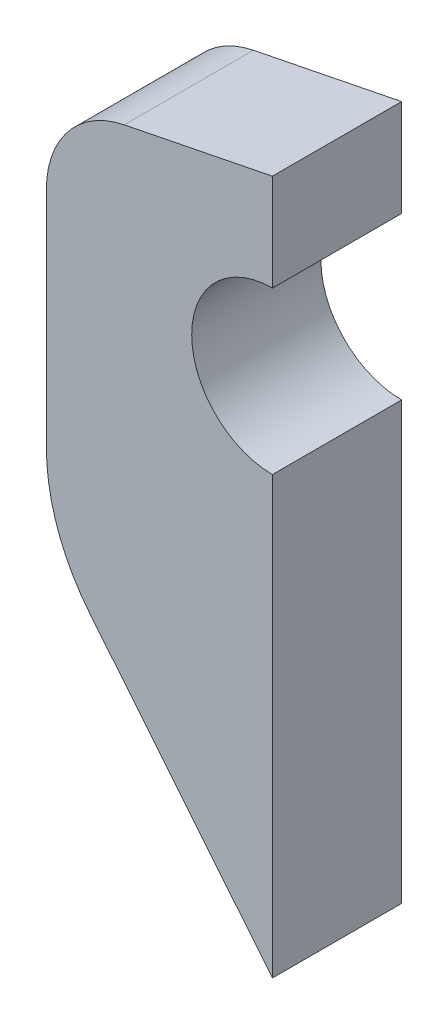
SolidWorks part; units mm, degrees
material "ﾊﾞﾙｻ"
ref_plane "正面" through (0, 0, 0) normal (0, 0, 1) x (1, 0, 0)
ref_plane "平面" through (0, 0, 0) normal (0, 1, 0) x (1, 0, 0)
ref_plane "右側面" through (0, 0, 0) normal (1, 0, 0) x (0, 0, -1)
sketch "ｽｹｯﾁ1" plane through (0, 0, 0) normal (0, 0, 1) x (1, 0, 0)
  line L0 (0, 5.5) -> (-15, 2.5)
  line L1 (-15, 2.5) -> (-15, -16)
  line L2 (-15, -16) -> (0, -16)
  line L3 (0, -16) -> (0, 5.5)
  line L4 (-15, 2.5) -> (0, 2.5) construction
  line L9 (0, -16) -> (-7, -7.4)
  line L10 (-7, -7.4) -> (-7, 4.1)
  circle A0 centre (0, 0) radius 2.5
  point P7 (-6.3571, -7.7069)
  point P8 (-10, -6)
  dimension "D1" = 5
  dimension "D2" = 10
  dimension "D3" = 3
  dimension "D4" = 15
  dimension "D5" = 6
  dimension "D6" = 16
  dimension "D7" = 7
  dimension "D8" = 11.5
extrude "ﾎﾞｽ - 押し出し1" add sketch "ｽｹｯﾁ1" along normal blind 4 contours L4 L10 L9 L3 A0 | L10 L4 L3 L0
fillet "ﾌｨﾚｯﾄ1" radius 3 1 edges at (-7, 4.1, 2)
fillet "ﾌｨﾚｯﾄ2" radius 6 1 edges at (-7, -7.4, 2)
